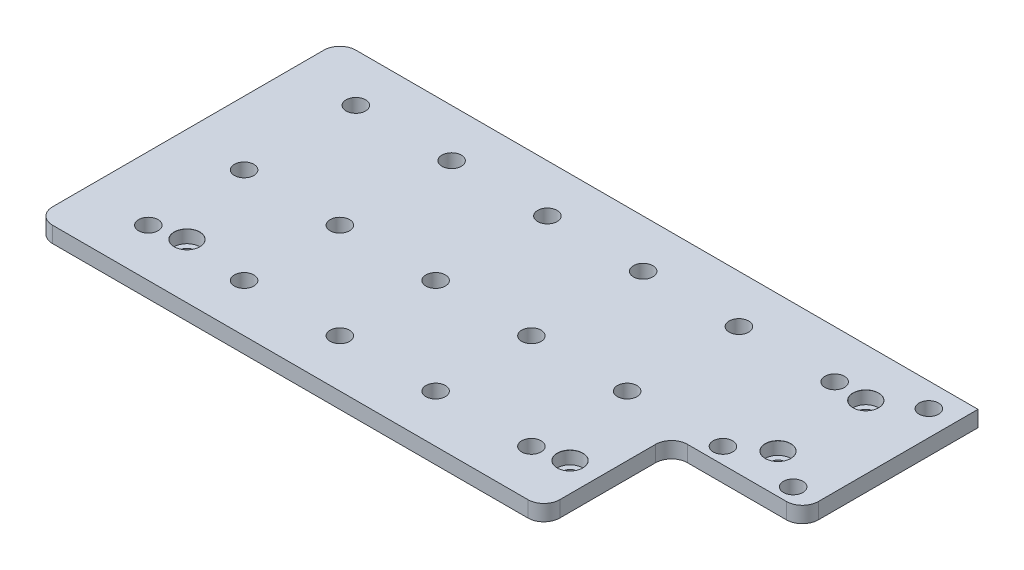
SolidWorks part; units mm, degrees
ref_plane "Front Plane" through (0, 0, 0) normal (0, 0, 1) x (1, 0, 0)
ref_plane "Top Plane" through (0, 0, 0) normal (0, 1, 0) x (1, 0, 0)
ref_plane "Right Plane" through (0, 0, 0) normal (1, 0, 0) x (0, 0, -1)
sketch "Sketch1" plane through (0, 0, 0) normal (0, 1, 0) x (1, 0, 0)
  line L1 (0, 0) -> (199.9, 0)
  line L2 (0, 0) -> (0, -95)
  line L3 (0, -95) -> (199.9, -95)
  line L4 (199.9, 0) -> (199.9, -95)
  dimension "D1" = 199.9
  dimension "D2" = 95
extrude "Boss-Extrude1" add sketch "Sketch1" along normal blind 5
sketch "Sketch2" plane through (0, 5, 0) normal (0, 1, 0) x (1, 0, 0)
  line L0 (0, -77.8) -> (199.9, -77.8) construction
  line L1 (0, 0) -> (0, -95) construction
  line L2 (179.9, 0) -> (179.9, -57.8) construction
  line L3 (199.9, 0) -> (0, 0) construction
  line L4 (0, -95) -> (199.9, -95) construction
  line L5 (199.9, -95) -> (199.9, 0) construction
  line L6 (179.9, -57.8) -> (199.9, -57.8) construction
  line L7 (179.9, -28.9) -> (199.9, -28.9) construction
  point P5 (149.9, -77.8)
  point P17 (29.9, -77.8)
  point P19 (179.9, -42.65)
  point P20 (179.9, -15.15)
  point P22 (69.9, -77.8) [skipped]
  point P24 (109.9, -77.8) [skipped]
  dimension "D1" = 17.2
  dimension "D2" = 20
  dimension "D3" = 37.2
  dimension "D4" = 50
  dimension "D6" = 27.5
  dimension "D5" = 4
hole_wizard "CBORE for M4 SHCS1" positions "Sketch2" profile "Sketch3" counterbore size "M4" standard "ANSI Metric"
sketch "Sketch3" plane through (179.9, 5, 15.15) normal (1, 0, 0) x (0, 0, 1)
  line L0 (0, 0) -> (0, 5)
  line L1 (0, 5) -> (2.25, 5)
  line L3 (2.25, 5) -> (2.25, 4)
  line L4 (4, 4) -> (2.25, 4)
  line L5 (4, 4) -> (4, 0.025)
  line L6 (4, 0.025) -> (4.025, 0)
  line L7 (4.025, 0) -> (0, 0)
  line L8 (-4, 0.025) -> (-4.025, 0) construction
  line L11 (0, -6.35) -> (0, 107.95) construction
  dimension "Thru Hole Dia." = 4.5
  dimension "Thru Hole Depth" = 5
  dimension "C'Bore Dia." = 8
  dimension "C'Bore Depth" = 4
  dimension "Near C'Sink Dia." = 8.05
  dimension "Near C'Sink Angle" = 90
sketch "Sketch4" plane through (0, 5, 0) normal (0, 1, 0) x (1, 0, 0)
  line L0 (0, -15) -> (200.6419, -15) construction
  line L1 (0, 0) -> (0, -95) construction
  line L2 (199.9, 0) -> (0, 0) construction
  point P4 (20, -15)
  point P7 (50, -15)
  point P9 (80, -15)
  point P10 (110, -15)
  point P11 (140, -15)
  point P12 (170, -15)
  dimension "D1" = 15
  dimension "D2" = 20
  dimension "D3" = 6
hole_wizard "Ø6.1 (6.1) Diameter Hole1" positions "Sketch4" profile "Sketch5" hole size "Ø6.1" standard "ANSI Metric" end condition through all
sketch "Sketch5" plane through (170, 5, 15) normal (1, 0, 0) x (0, 0, 1)
  line L0 (0, 0) -> (0, 5)
  line L1 (0, 5) -> (3.05, 5)
  line L2 (3.05, 5) -> (3.05, 0)
  line L5 (3.05, 0) -> (0, 0)
  line L11 (0, -6.35) -> (0, 107.95) construction
  dimension "Thru Hole Dia." = 6.1
  dimension "Thru Hole Depth" = 5
pattern_linear "LPattern1" count 2 spacing 35 along (0, 0, 1) of "Ø6.1 (6.1) Diameter Hole1"
sketch "Sketch6" plane through (0, 5, 0) normal (0, 1, 0) x (1, 0, 0)
  line L1 (199.9, -95) -> (158.9, -95)
  line L2 (199.9, -95) -> (199.9, -55)
  line L3 (199.9, -55) -> (158.9, -55)
  line L4 (158.9, -95) -> (158.9, -55)
  dimension "D1" = 41
  dimension "D2" = 40
extrude "Cut-Extrude1" cut sketch "Sketch6" against normal through all
pattern_linear "LPattern2" count 2 spacing 65 along (0, 0, 1) of "Ø6.1 (6.1) Diameter Hole1"
fillet "Fillet1" radius 5 3 edges at (158.9, 2.5, 55) (199.9, 2.5, 55) (158.9, 2.5, 95)
sketch "Sketch7" plane through (0, 5, 0) normal (0, 1, 0) x (1, 0, 0)
  line L1 (170, -50) -> (192, -50) construction
  line L2 (192, -7.5) -> (192, -50) construction
  line L3 (199.9, -50) -> (199.9, 0) construction
  point P7 (192, -7.5)
  point P8 (192, -50)
  dimension "D1" = 42.5
  dimension "D2" = 7.9
hole_wizard "Ø6.1 (6.1) Diameter Hole2" positions "Sketch7" profile "Sketch8" hole size "Ø6.1" standard "ANSI Metric" end condition through all
sketch "Sketch8" plane through (192, 5, 50) normal (1, 0, 0) x (0, 0, 1)
  line L0 (0, 0) -> (0, 5)
  line L1 (0, 5) -> (3.05, 5)
  line L2 (3.05, 5) -> (3.05, 0)
  line L5 (3.05, 0) -> (0, 0)
  line L11 (0, -6.35) -> (0, 107.95) construction
  dimension "Thru Hole Dia." = 6.1
  dimension "Thru Hole Depth" = 5
fillet "Fillet2" radius 5 2 edges at (0, 2.5, 95) (0, 2.5, 0)
